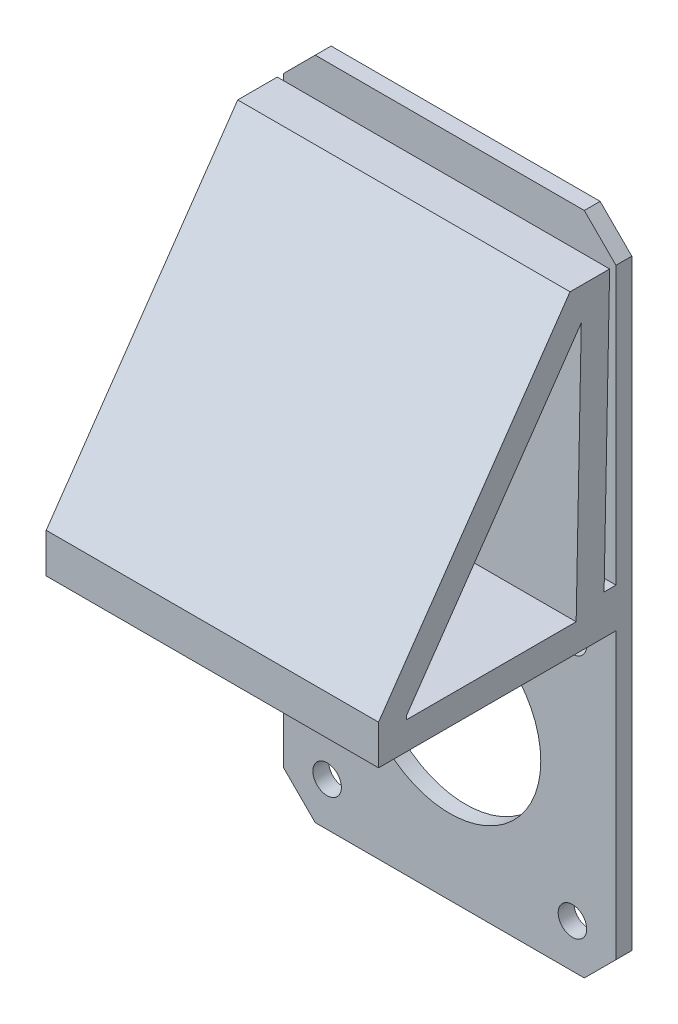
SolidWorks part; units mm, degrees
ref_plane "Front Plane" through (0, 0, 0) normal (0, 0, 1) x (1, 0, 0)
ref_plane "Top Plane" through (0, 0, 0) normal (0, 1, 0) x (1, 0, 0)
ref_plane "Right Plane" through (0, 0, 0) normal (1, 0, 0) x (0, 0, -1)
sketch "Sketch1" plane through (0, 0, 0) normal (0, 0, 1) x (1, 0, 0)
  line L0 (0, 0) -> (0, -21) construction
  line L1 (-21, -21) -> (21, -21)
  line L2 (-21, -21) -> (-21, 63)
  line L3 (-21, 63) -> (21, 63)
  line L4 (21, -21) -> (21, 63)
  line L5 (0, 0) -> (21, 0) construction
  circle A0 centre (0, 0) radius 11.5
  dimension "D1" = 23
  dimension "D2" = 42
  dimension "D3" = 84
extrude "Boss-Extrude1" add sketch "Sketch1" along normal blind 2
hole_wizard "M3 Clearance Hole1" positions "Sketch2" profile "Sketch3" hole size "M3" standard "ANSI Metric" end condition through all
sketch "Sketch2" plane through (0, 0, 2) normal (0, 0, 1) x (1, 0, 0)
  line L0 (-15.5, 15.5) -> (15.5, -15.5) construction
  line L3 (15.5, 15.5) -> (-15.5, -15.5) construction
  point P0 (-15.5, 15.5)
  point P2 (15.5, 15.5)
  point P4 (15.5, -15.5)
  point P6 (-15.5, -15.5)
  dimension "D1" = 31
  dimension "D2" = 31
sketch "Sketch3" plane through (-15.5, 15.5, 2) normal (1, 0, 0) x (0, -1, 0)
  line L0 (0, 0) -> (0, 2)
  line L1 (0, 2) -> (1.8, 2)
  line L2 (1.8, 2) -> (1.8, 0)
  line L5 (1.8, 0) -> (0, 0)
  line L11 (0, -6.35) -> (0, 107.95) construction
  dimension "Thru Hole Dia." = 3.6
  dimension "Thru Hole Depth" = 2
chamfer "Chamfer1" distance 4 angle 45 4 edges at (-21, 63, 1) (21, 63, 1) (21, -21, 1) (-21, -21, 1)
sketch "Sketch4" plane through (21, 0, 0) normal (1, 0, 0) x (0, 0, -1)
  line L0 (-32, 24) -> (-7.8, 59)
  line L1 (-2, 24) -> (-3.5, 24)
  line L2 (-2, 24) -> (-2, 19)
  line L3 (-2, 19) -> (-32, 19)
  line L4 (-32, 24) -> (-32, 19)
  line L5 (-2, 24) -> (-32, 19) construction
  line L6 (-2, 19) -> (-32, 24) construction
  line L7 (-2, -17) -> (-2, 59) construction
  line L8 (0, 59) -> (-2, 59) construction
  line L9 (-7.8, 59) -> (-2.8, 59)
  line L10 (-2.8, 59) -> (-3.5, 24)
  line L12 (-2, -17) -> (-2, 59) construction
  point P4 (-17, 21.5)
  point P14 (-3.5, 58.8185)
  point P15 (0, 0)
  dimension "D1" = 35
  dimension "D2" = 5
  dimension "D3" = 30
  dimension "D4" = 1.5
  dimension "D5" = 0.8
  dimension "D6" = 5
  dimension "D7" = 35
extrude "Boss-Extrude2" add sketch "Sketch4" against normal through all
sketch "Sketch5" plane through (-21, 0, 0) normal (-1, 0, 0) x (0, 0, 1)
  line L22 (7.0307, 22.5) -> (28.5, 22.5)
  line L23 (28.5, 22.5) -> (28.5, 22.9078)
  line L24 (28.5, 22.9078) -> (6.3828, 54.8955)
  line L26 (6.3828, 54.8955) -> (7.0307, 22.5)
  line L27 (7.0307, 22.5) -> (28.5, 22.5)
  line L28 (28.5, 22.5) -> (28.5, 22.9078)
  line L29 (28.5, 22.9078) -> (6.3828, 54.8955)
  line L31 (6.3828, 54.8955) -> (7.0307, 22.5)
  dimension "D1" = 3.5
extrude "Cut-Extrude4" cut sketch "Sketch5" against normal through all
